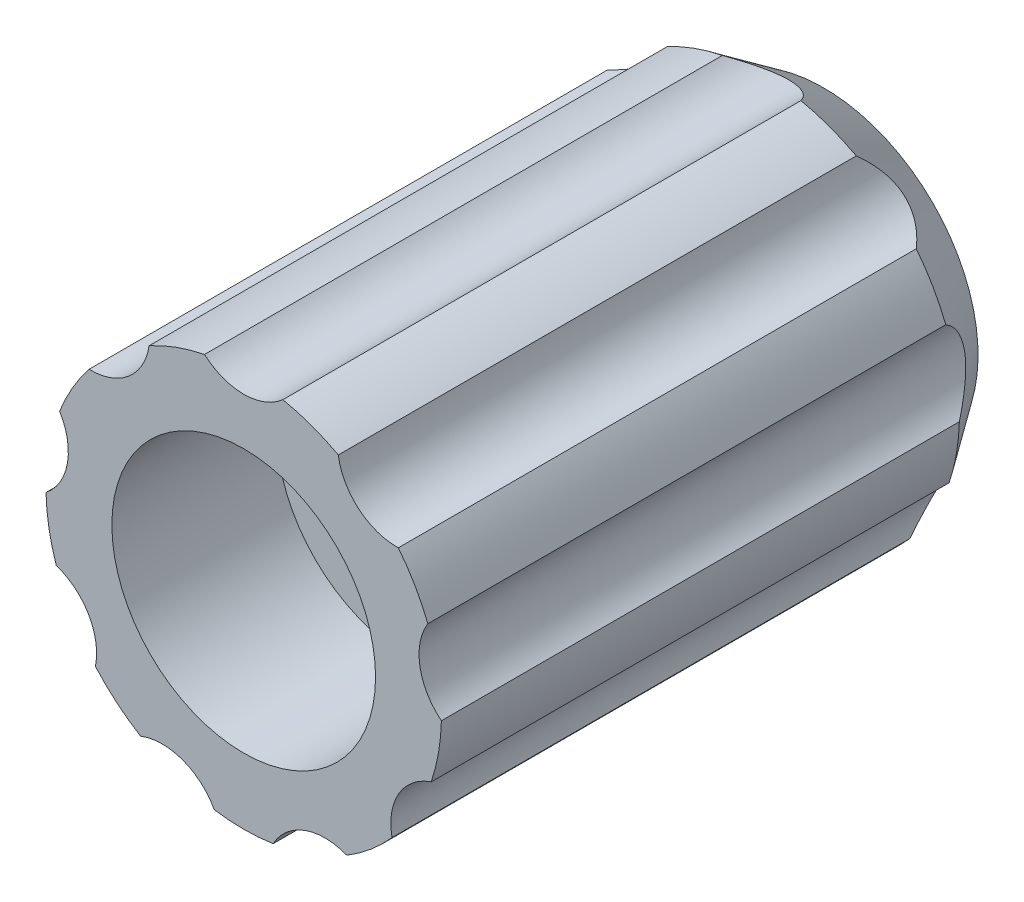
SolidWorks part; units mm, degrees
ref_plane "Front Plane" through (0, 0, 0) normal (0, 0, 1) x (1, 0, 0)
ref_plane "Top Plane" through (0, 0, 0) normal (0, 1, 0) x (1, 0, 0)
ref_plane "Right Plane" through (0, 0, 0) normal (1, 0, 0) x (0, 0, -1)
sketch "Skica1" plane through (0, 0, 0) normal (0, 0, 1) x (1, 0, 0)
  line L0 (-2.5249, -1.575) -> (2.5249, -1.575)
  arc A0 (2.7005, -1.4707) -> (-2.7005, -1.4707) centre (0, 0) ccw
  arc A2 (2.5249, -1.575) -> (2.7005, -1.4707) centre (2.5249, -1.375) ccw
  arc A3 (-2.5249, -1.575) -> (-2.7005, -1.4707) centre (-2.5249, -1.375) cw
  circle A7 centre (0, 0) radius 6
  dimension "D1" = 6.15
  dimension "D3" = 0.2
  dimension "D4" = 12
  dimension "D2" = 4.65
extrude "Přidat vysunutím1" add sketch "Skica1" along normal blind 7
sketch "Skica5" plane through (0, 0, 7) normal (0, 0, 1) x (1, 0, 0)
  circle A0 centre (0, 0) radius 4
  circle A1 centre (0, 0) radius 6
  dimension "D1" = 8
  dimension "D2" = 12
extrude "Přidat vysunutím3" add sketch "Skica5" along normal blind 5
sketch "Skica6" plane through (0, 0, 0) normal (0, 0, -1) x (-1, 0, 0)
  circle A0 centre (0, 0) radius 6
  dimension "D1" = 12
extrude "Přidat vysunutím4" add sketch "Skica6" along normal blind 0.6
ref_plane "Rovina1" through (0, 0, 5) normal (0, 0, 1) x (1, 0, 0)
sketch "Skica7" plane through (0, 0, 5) normal (0, 0, 1) x (1, 0, 0)
  line L0 (-2.5249, -1.575) -> (2.5249, -1.575) construction
  circle A0 centre (0, -2.7418) radius 1.2668
  dimension "D1" = 0.1
extrude "Přidat vysunutím5" add sketch "Skica7" against normal blind 1
sketch "Skica8" plane through (0, 0, 12) normal (0, 0, 1) x (1, 0, 0)
  circle A0 centre (0, 7.2222) radius 1.7925
  circle A1 centre (4.6424, 5.5325) radius 1.7925
  circle A2 centre (7.1125, 1.2541) radius 1.7925
  circle A3 centre (6.2546, -3.6111) radius 1.7925
  circle A4 centre (2.4701, -6.7867) radius 1.7925
  circle A5 centre (-2.4701, -6.7867) radius 1.7925
  circle A6 centre (-6.2546, -3.6111) radius 1.7925
  circle A7 centre (-7.1125, 1.2541) radius 1.7925
  circle A8 centre (-4.6424, 5.5325) radius 1.7925
  point P20 (0, 0)
  dimension "D1" = 9
extrude "Odebrat vysunutím2" cut sketch "Skica8" against normal blind 21
sketch "Skica9" plane through (0, 0, 0) normal (0, 1, 0) x (1, 0, 0)
  line L0 (0, 0) -> (-11.4454, 0) construction
sketch "Skica11" plane through (0, 0, 7) normal (0, 0, 1) x (1, 0, 0)
  line L3 (-2.5249, -1.645) -> (2.5249, -1.645)
  line L4 (-2.5249, -1.645) -> (2.5249, -1.645)
  arc A11 (2.5249, -1.645) -> (2.762, -1.5041) centre (2.5249, -1.375) ccw
  arc A12 (-2.762, -1.5041) -> (-2.5249, -1.645) centre (-2.5249, -1.375) ccw
  arc A13 (2.762, -1.5041) -> (-2.762, -1.5041) centre (0, 0) ccw
  arc A14 (2.5249, -1.645) -> (2.762, -1.5041) centre (2.5249, -1.375) ccw
  arc A15 (-2.762, -1.5041) -> (-2.5249, -1.645) centre (-2.5249, -1.375) ccw
  arc A16 (2.762, -1.5041) -> (-2.762, -1.5041) centre (0, 0) ccw
  dimension "D1" = 0.07
extrude "Odebrat vysunutím4" cut sketch "Skica11" against normal up to surface (7 mm away) up to face at (0, -0.3985, 0)
sketch "Skica12" plane through (0, 0, 0) normal (1, 0, 0) x (0, 0, -1)
  line L0 (-2, -1.645) -> (0, -1.495)
  line L1 (0, -1.645) -> (-7, -1.645) construction
  line L2 (0, 3.145) -> (0, -1.5041) construction
  line L3 (0, -1.495) -> (0, -1.645)
  line L4 (0, -1.645) -> (-2, -1.645)
  dimension "D1" = 0.15
  dimension "D2" = 2
extrude "Přidat vysunutím6" add sketch "Skica12" along normal mid plane 1
sketch "Skica13" plane through (0, 0, -0.6) normal (0, 0, -1) x (-1, 0, 0)
  arc A18 (2.8693, 5.2694) -> (4.6911, 3.7407) centre (4.6424, 5.5325) ccw
  arc A19 (2.8693, 5.2694) -> (1.1891, 5.881) centre (0, 0) ccw
  arc A20 (-1.1891, 5.881) -> (1.1891, 5.881) centre (0, 7.2222) ccw
  arc A21 (-1.1891, 5.881) -> (-2.8693, 5.2694) centre (0, 0) ccw
  arc A22 (-4.6911, 3.7407) -> (-2.8693, 5.2694) centre (-4.6424, 5.5325) ccw
  arc A23 (-4.6911, 3.7407) -> (-5.5852, 2.1923) centre (0, 0) ccw
  arc A24 (-5.9981, -0.1498) -> (-5.5852, 2.1923) centre (-7.1125, 1.2541) ccw
  arc A25 (-5.9981, -0.1498) -> (-5.6876, -1.9107) centre (0, 0) ccw
  arc A26 (-4.4985, -3.9703) -> (-5.6876, -1.9107) centre (-6.2546, -3.6111) ccw
  arc A27 (-4.4985, -3.9703) -> (-3.1288, -5.1196) centre (0, 0) ccw
  arc A28 (-0.894, -5.933) -> (-3.1288, -5.1196) centre (-2.4701, -6.7867) ccw
  arc A29 (-0.894, -5.933) -> (0.894, -5.933) centre (0, 0) ccw
  arc A30 (3.1288, -5.1196) -> (0.894, -5.933) centre (2.4701, -6.7867) ccw
  arc A31 (3.1288, -5.1196) -> (4.4985, -3.9703) centre (0, 0) ccw
  arc A32 (5.6876, -1.9107) -> (4.4985, -3.9703) centre (6.2546, -3.6111) ccw
  arc A33 (5.6876, -1.9107) -> (5.9981, -0.1498) centre (0, 0) ccw
  arc A34 (5.5852, 2.1923) -> (5.9981, -0.1498) centre (7.1125, 1.2541) ccw
  arc A35 (5.5852, 2.1923) -> (4.6911, 3.7407) centre (0, 0) ccw
  arc A36 (2.8693, 5.2694) -> (4.6911, 3.7407) centre (4.6424, 5.5325) ccw
  arc A37 (2.8693, 5.2694) -> (1.1891, 5.881) centre (0, 0) ccw
  arc A38 (-1.1891, 5.881) -> (1.1891, 5.881) centre (0, 7.2222) ccw
  arc A39 (-1.1891, 5.881) -> (-2.8693, 5.2694) centre (0, 0) ccw
  arc A40 (-4.6911, 3.7407) -> (-2.8693, 5.2694) centre (-4.6424, 5.5325) ccw
  arc A41 (-4.6911, 3.7407) -> (-5.5852, 2.1923) centre (0, 0) ccw
  arc A42 (-5.9981, -0.1498) -> (-5.5852, 2.1923) centre (-7.1125, 1.2541) ccw
  arc A43 (-5.9981, -0.1498) -> (-5.6876, -1.9107) centre (0, 0) ccw
  arc A44 (-4.4985, -3.9703) -> (-5.6876, -1.9107) centre (-6.2546, -3.6111) ccw
  arc A45 (-4.4985, -3.9703) -> (-3.1288, -5.1196) centre (0, 0) ccw
  arc A46 (-0.894, -5.933) -> (-3.1288, -5.1196) centre (-2.4701, -6.7867) ccw
  arc A47 (-0.894, -5.933) -> (0.894, -5.933) centre (0, 0) ccw
  arc A48 (3.1288, -5.1196) -> (0.894, -5.933) centre (2.4701, -6.7867) ccw
  arc A49 (3.1288, -5.1196) -> (4.4985, -3.9703) centre (0, 0) ccw
  arc A50 (5.6876, -1.9107) -> (4.4985, -3.9703) centre (6.2546, -3.6111) ccw
  arc A51 (5.6876, -1.9107) -> (5.9981, -0.1498) centre (0, 0) ccw
  arc A52 (5.5852, 2.1923) -> (5.9981, -0.1498) centre (7.1125, 1.2541) ccw
  arc A53 (5.5852, 2.1923) -> (4.6911, 3.7407) centre (0, 0) ccw
  dimension "D1" = 0
extrude "Přidat vysunutím7" add sketch "Skica13" along normal blind 5
sketch "Skica14" plane through (0, 0, 0) normal (0, 1, 0) x (1, 0, 0)
  line L0 (-0.5194, 11.5402) -> (-8.8739, -0.3913)
  line L1 (-8.8739, -0.3913) -> (-8.3061, 8.7261)
  line L2 (-8.3061, 8.7261) -> (-0.5194, 11.5402)
  line L3 (0, 0) -> (0, 7.4717) construction
  dimension "D1" = 35
revolve "Odebrat rotací1" cut sketch "Skica14" angle 360 about L3
